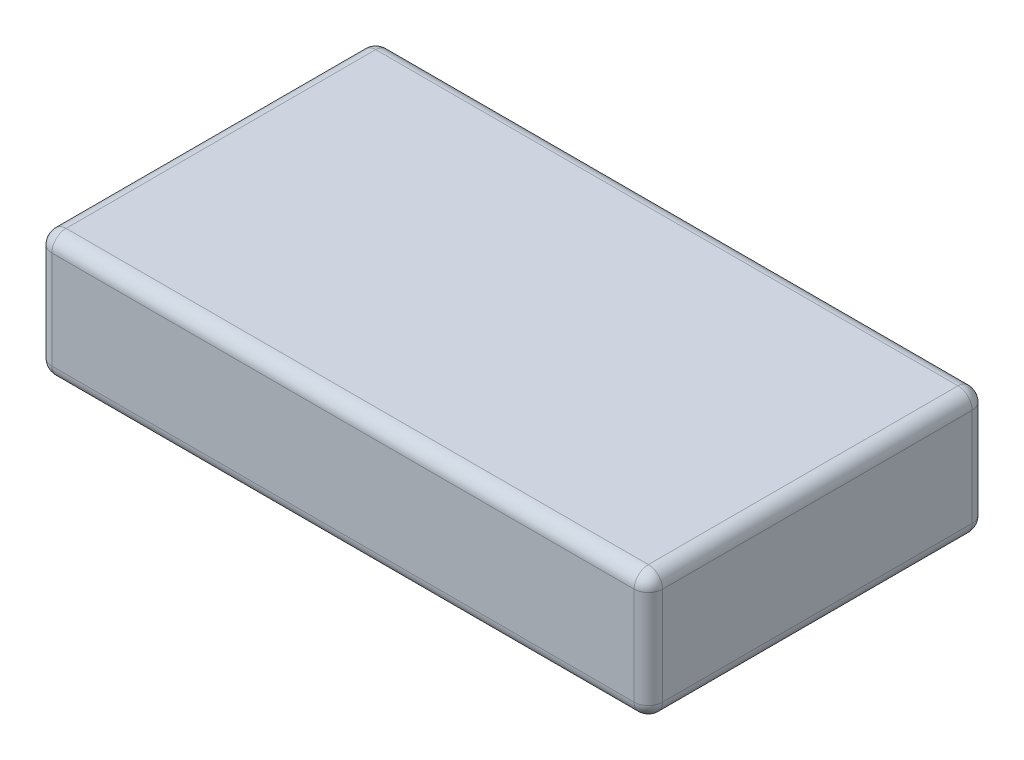
SolidWorks part; units mm, degrees
ref_plane "Front Plane" through (0, 0, 0) normal (0, 0, 1) x (1, 0, 0)
ref_plane "Top Plane" through (0, 0, 0) normal (0, 1, 0) x (1, 0, 0)
ref_plane "Right Plane" through (0, 0, 0) normal (1, 0, 0) x (0, 0, -1)
sketch "Sketch1" plane through (0, 0, 0) normal (0, 1, 0) x (1, 0, 0)
  line L1 (-20.5, -11.9) -> (20.5, -11.9)
  line L2 (-21.5, -10.9) -> (-21.5, 10.9)
  line L3 (-20.5, 11.9) -> (20.5, 11.9)
  line L4 (21.5, -10.9) -> (21.5, 10.9)
  line L5 (-21.5, -11.9) -> (21.5, 11.9) construction
  line L6 (-21.5, 11.9) -> (21.5, -11.9) construction
  arc A0 (-20.5, -11.9) -> (-21.5, -10.9) centre (-20.5, -10.9) cw
  arc A1 (20.5, -11.9) -> (21.5, -10.9) centre (20.5, -10.9) ccw
  arc A2 (20.5, 11.9) -> (21.5, 10.9) centre (20.5, 10.9) cw
  arc A3 (-21.5, 10.9) -> (-20.5, 11.9) centre (-20.5, 10.9) cw
  point P0 (0, 0)
  dimension "D3" = 1
  dimension "D1" = 43
  dimension "D2" = 23.8
extrude "Boss-Extrude1" add sketch "Sketch1" along normal blind 8.89
fillet "Fillet1" radius 1 16 edges at (0, 0, 11.9) (21.2071, 0, 11.6071) (21.5, 0, 0) (21.2071, 0, -11.6071) (0, 0, -11.9) (-21.2071, 0, -11.6071) (-21.5, 0, 0) (-21.2071, 0, 11.6071) (-21.5, 8.89, 0) (-21.2071, 8.89, -11.6071) (0, 8.89, -11.9) (21.2071, 8.89, -11.6071) (21.5, 8.89, 0) (21.2071, 8.89, 11.6071) (0, 8.89, 11.9) (-21.2071, 8.89, 11.6071)
